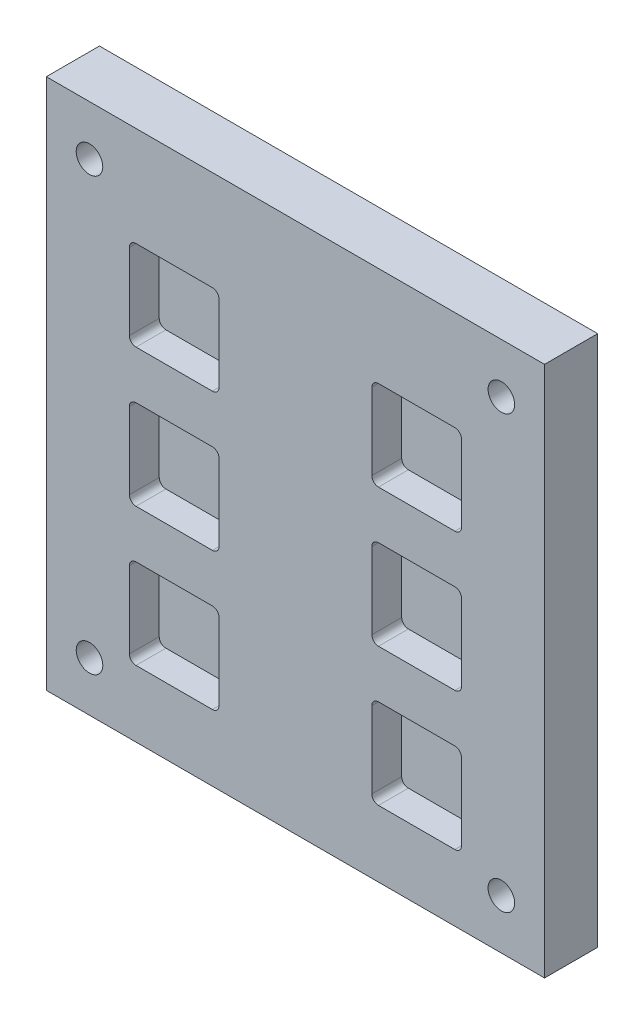
SolidWorks part; units mm, degrees
ref_plane "Front Plane" through (0, 0, 0) normal (0, 0, 1) x (1, 0, 0)
ref_plane "Top Plane" through (0, 0, 0) normal (0, 1, 0) x (1, 0, 0)
ref_plane "Right Plane" through (0, 0, 0) normal (1, 0, 0) x (0, 0, -1)
sketch "Sketch1" plane through (0, 0, 0) normal (0, 0, 1) x (1, 0, 0)
  line L0 (0, 0) -> (0, 63073.7852) construction
  line L1 (0, 0) -> (-63073.7852, 0) construction
  line L3 (75, -80) -> (-75, -80)
  line L4 (75, -80) -> (75, 80)
  line L5 (75, 80) -> (-75, 80)
  line L6 (-75, -80) -> (-75, 80)
  line L7 (75, -80) -> (-75, 80) construction
  line L8 (75, 80) -> (-75, -80) construction
  point P5 (0, 0)
  dimension "D1" = 150
  dimension "D2" = 160
extrude "Boss-Extrude1" add sketch "Sketch1" along normal blind 16
sketch "Sketch2" plane through (0, 0, 16) normal (0, 0, 1) x (1, 0, 0)
  line L0 (0, 0) -> (0, 50000) construction
  line L1 (0, 0) -> (-50000, 0) construction
  line L2 (75, 80) -> (-75, 80) construction
  line L3 (-48, 23) -> (-25, 23)
  line L4 (-50, 25) -> (-50, 48)
  line L5 (-48, 50) -> (-25, 50)
  line L6 (-23, 25) -> (-23, 48)
  line L7 (-50, 23) -> (-23, 50) construction
  line L8 (-50, 50) -> (-23, 23) construction
  line L9 (-75, 80) -> (-75, -80) construction
  line L10 (50, 50) -> (23, 23) construction
  line L11 (50, 23) -> (23, 50) construction
  line L12 (23, 25) -> (23, 48)
  line L13 (48, 50) -> (25, 50)
  line L14 (50, 25) -> (50, 48)
  line L15 (48, 23) -> (25, 23)
  line L17 (-48, -60) -> (-25, -60)
  line L18 (-50, -58) -> (-50, -35)
  line L19 (-48, -33) -> (-25, -33)
  line L20 (-23, -58) -> (-23, -35)
  line L21 (-50, -60) -> (-23, -33) construction
  line L22 (-50, -33) -> (-23, -60) construction
  line L23 (-75, -80) -> (75, -80) construction
  line L24 (50, -33) -> (23, -60) construction
  line L25 (50, -60) -> (23, -33) construction
  line L26 (23, -58) -> (23, -35)
  line L27 (48, -33) -> (25, -33)
  line L28 (50, -58) -> (50, -35)
  line L29 (48, -60) -> (25, -60)
  line L33 (23, 8.5) -> (50, -18.5) construction
  line L34 (-25, -18.5) -> (-48, -18.5)
  line L35 (-23, -16.5) -> (-23, 6.5)
  line L36 (-25, 8.5) -> (-48, 8.5)
  line L41 (-50, -16.5) -> (-50, 6.5)
  line L42 (-23, -18.5) -> (-50, 8.5) construction
  line L43 (-23, 8.5) -> (-50, -18.5) construction
  line L44 (23, -18.5) -> (50, 8.5) construction
  line L45 (50, -16.5) -> (50, 6.5)
  line L46 (25, 8.5) -> (48, 8.5)
  line L47 (23, -16.5) -> (23, 6.5)
  line L48 (25, -18.5) -> (48, -18.5)
  arc A0 (50, 48) -> (48, 50) centre (48, 48) ccw
  arc A1 (25, 50) -> (23, 48) centre (25, 48) ccw
  arc A2 (25, 23) -> (23, 25) centre (25, 25) cw
  arc A3 (48, 23) -> (50, 25) centre (48, 25) ccw
  arc A8 (48, -60) -> (50, -58) centre (48, -58) ccw
  arc A9 (50, -35) -> (48, -33) centre (48, -35) ccw
  arc A10 (25, -33) -> (23, -35) centre (25, -35) ccw
  arc A11 (25, -60) -> (23, -58) centre (25, -58) cw
  arc A12 (-25, -60) -> (-23, -58) centre (-25, -58) ccw
  arc A13 (-48, -60) -> (-50, -58) centre (-48, -58) cw
  arc A14 (-50, -35) -> (-48, -33) centre (-48, -35) cw
  arc A15 (-25, -33) -> (-23, -35) centre (-25, -35) cw
  arc A20 (-25, 23) -> (-23, 25) centre (-25, 25) ccw
  arc A21 (-48, 23) -> (-50, 25) centre (-48, 25) cw
  arc A22 (-50, 48) -> (-48, 50) centre (-48, 48) cw
  arc A23 (-25, 50) -> (-23, 48) centre (-25, 48) cw
  arc A24 (-23, 6.5) -> (-25, 8.5) centre (-25, 6.5) ccw
  arc A25 (-25, -18.5) -> (-23, -16.5) centre (-25, -16.5) ccw
  arc A26 (-48, -18.5) -> (-50, -16.5) centre (-48, -16.5) cw
  arc A27 (-48, 8.5) -> (-50, 6.5) centre (-48, 6.5) ccw
  arc A28 (48, 8.5) -> (50, 6.5) centre (48, 6.5) cw
  arc A29 (48, -18.5) -> (50, -16.5) centre (48, -16.5) ccw
  arc A30 (25, -18.5) -> (23, -16.5) centre (25, -16.5) cw
  arc A31 (23, 6.5) -> (25, 8.5) centre (25, 6.5) cw
  point P5 (-36.5, 36.5)
  point P18 (36.5, 36.5)
  point P19 (-36.5, -46.5)
  point P30 (36.5, -46.5)
  point P31 (-36.5, -5)
  point P100 (36.5, -5)
  dimension "D10" = 2
  dimension "D12" = 2
  dimension "D14" = 2
  dimension "D15" = 2
  dimension "D1" = 30
  dimension "D2" = 25
  dimension "D3" = 27
  dimension "D4" = 25
  dimension "D5" = 20
  dimension "D6" = 27
  dimension "D7" = 27
  dimension "D9" = 28
  dimension "D11" = 23
  dimension "D8" = 27
  dimension "D13" = 25
extrude "Cut-Extrude1" cut sketch "Sketch2" against normal blind 9
sketch "Sketch3" plane through (0, 0, 16) normal (0, 0, 1) x (1, 0, 0)
  line L0 (0, 0) -> (0, 50000) construction
  line L1 (0, 0) -> (-50000, 0) construction
  circle A0 centre (-62, 65) radius 4
  circle A1 centre (62, 65) radius 4
  circle A2 centre (62, -65) radius 4
  circle A3 centre (-62, -65) radius 4
  point P7 (0, 0)
  dimension "D1" = 8
  dimension "D2" = 62
  dimension "D3" = 65
extrude "Cut-Extrude2" cut sketch "Sketch3" against normal through all
